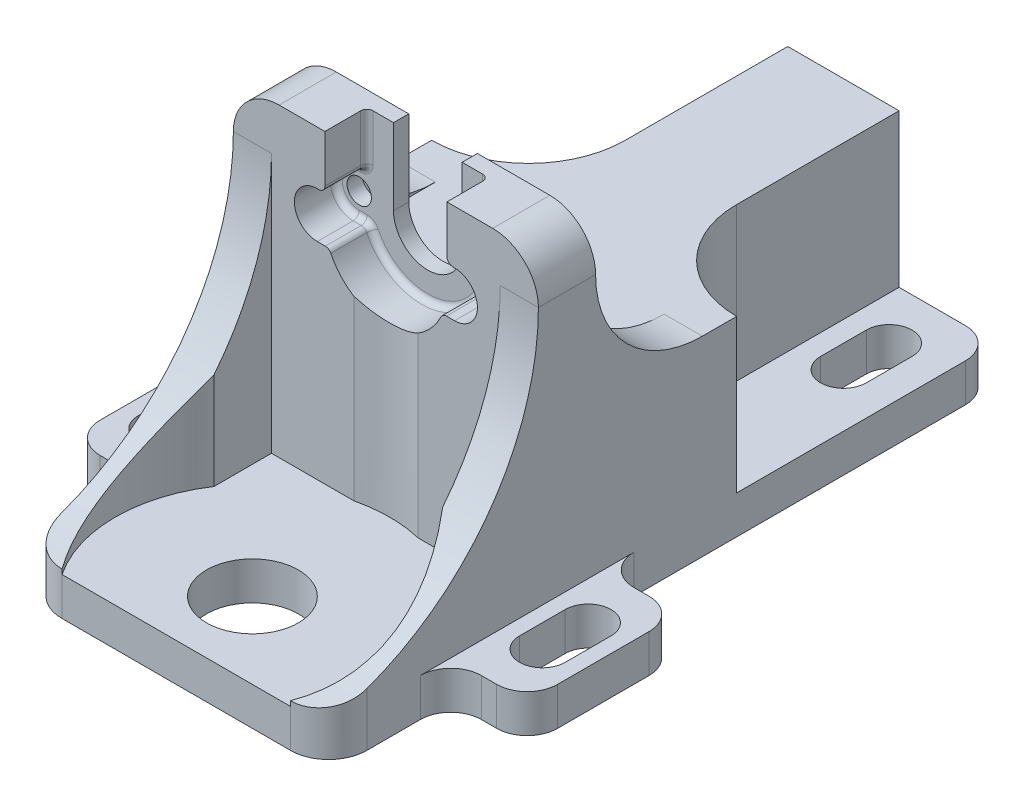
SolidWorks part; units mm, degrees
ref_plane "Front Plane" through (0, 0, 0) normal (0, 0, 1) x (1, 0, 0)
ref_plane "Top Plane" through (0, 0, 0) normal (0, 1, 0) x (1, 0, 0)
ref_plane "Right Plane" through (0, 0, 0) normal (1, 0, 0) x (0, 0, -1)
sketch "Sketch1" plane through (0, 0, 0) normal (0, 1, 0) x (1, 0, 0)
  line L1 (10, -25) -> (-10, -25)
  line L2 (10, -25) -> (10, 25)
  line L3 (10, 25) -> (-10, 25)
  line L4 (-10, -25) -> (-10, 25)
  line L5 (10, -25) -> (-10, 25) construction
  line L6 (10, 25) -> (-10, -25) construction
  point P0 (0, 0)
  dimension "D1" = 50
  dimension "D2" = 20
extrude "Boss-Extrude1" add sketch "Sketch1" along normal blind 12.525
sketch "Sketch2" plane through (0, 12.525, 0) normal (0, 1, 0) x (1, 0, 0)
  line L0 (-10, 25) -> (-10, -25) construction
  line L1 (-10, -1.25) -> (10, -1.25)
  line L2 (-10, -1.25) -> (-10, -5)
  line L3 (-10, -5) -> (10, -5)
  line L4 (10, -1.25) -> (10, -5)
  line L5 (10, -25) -> (10, 25) construction
  line L6 (-10, -25) -> (10, -25) construction
  dimension "D1" = 3.75
  dimension "D2" = 20
extrude "Boss-Extrude2" add sketch "Sketch2" along normal blind 10
sketch "Sketch3" plane through (0, 0, 5) normal (0, 0, 1) x (1, 0, 0)
  line L0 (-10, 22.525) -> (-10, 12.525) construction
  line L1 (-10, 12.525) -> (10, 12.525) construction
  line L2 (-10, 12.525) -> (-10, 22.525) construction
  line L3 (-10, 22.525) -> (10, 22.525) construction
  line L4 (10, 12.525) -> (10, 22.525) construction
  line L5 (-10, 12.525) -> (10, 22.525) construction
  line L6 (-10, 22.525) -> (10, 12.525) construction
  line L7 (-10, 12.525) -> (10, 12.525) construction
  line L8 (-4, 19.025) -> (-4, 22.525)
  line L9 (-4, 22.525) -> (4, 22.525)
  line L10 (4, 22.525) -> (4, 19.025)
  line L11 (0, 22.525) -> (0, 12.525) construction
  line L12 (-4.5, 17.525) -> (4.5, 17.525) construction
  line L13 (-4.5, 19.025) -> (-4, 19.025)
  line L14 (-4.5, 16.025) -> (-3.7081, 16.025)
  line L15 (4, 19.025) -> (4.5, 19.025)
  line L16 (3.7081, 16.025) -> (4.5, 16.025)
  line L17 (-4.5, 19.025) -> (-4.5, 16.025) construction
  arc A0 (-3.7081, 16.025) -> (3.7081, 16.025) centre (0, 17.525) ccw
  arc A3 (-4.5, 19.025) -> (-4.5, 16.025) centre (-4.5, 17.525) ccw
  arc A4 (4.5, 16.025) -> (4.5, 19.025) centre (4.5, 17.525) ccw
  point P20 (0, 11.35)
  dimension "D1" = 8
  dimension "D2" = 9
  dimension "D4" = 1.5
extrude "Cut-Extrude1" cut sketch "Sketch3" against normal offset from surface (2.75 mm away) 1 up to face at (2.5, 20.025, 1.25)
sketch "Sketch5" plane through (0, 0, 2.25) normal (0, 0, 1) x (1, 0, 0)
  line L0 (-2.25, 17.525) -> (-2.25, 22.525)
  line L1 (-4, 22.525) -> (4, 22.525) construction
  line L2 (-2.25, 22.525) -> (2.25, 22.525)
  line L3 (2.25, 22.525) -> (2.25, 17.525)
  arc A0 (-2.25, 17.525) -> (2.25, 17.525) centre (0, 17.525) ccw
  circle A1 centre (-4.5, 17.525) radius 0.8
  circle A2 centre (4.5, 17.525) radius 0.8
  dimension "D1" = 1.6
  dimension "D2" = 4.5
extrude "Cut-Extrude2" cut sketch "Sketch5" against normal through all
fillet "Fillet1" radius 0.4 13 edges at (4.104, 16.025, 2.25) (-4.104, 16.025, 2.25) (-4.25, 19.025, 2.25) (-4, 19.025, 3.625) (3.7081, 16.025, 3.625) (-3.7081, 16.025, 3.625) (6, 17.525, 2.25) (0, 13.525, 2.25) (-4, 20.775, 2.25) (-6, 17.525, 2.25) (4.25, 19.025, 2.25) (4, 19.025, 3.625) (4, 20.775, 2.25)
fillet "Fillet2" radius 3 2 edges at (10, 22.525, 3.125) (-10, 22.525, 3.125)
sketch "Sketch6" plane through (0, 12.525, 0) normal (0, 1, 0) x (1, 0, 0)
  line L2 (-10, -5) -> (10, -5)
  line L3 (-10, -5) -> (-10, -25)
  line L4 (-10, -25) -> (10, -25)
  line L5 (10, -5) -> (10, -25)
extrude "Cut-Extrude3" cut sketch "Sketch6" against normal offset from surface (10.025 mm away) 2.5 up to face at (0, 0, 0)
sketch "Sketch7" plane through (0, 2.5, 0) normal (0, 1, 0) x (1, 0, 0)
  line L1 (-2.25, -2.25) -> (2.25, -2.25) construction
  circle A0 centre (0, -13.75) radius 3.01
  dimension "D1" = 6.02
  dimension "D2" = 11.5
extrude "Cut-Extrude4" cut sketch "Sketch7" against normal through all
sketch "Sketch8" plane through (-10, 0, 0) normal (-1, 0, 0) x (0, 0, 1)
  line L0 (5, 19.525) -> (1.25, 19.525) construction
  line L1 (5, 2.5) -> (22.025, 2.5)
  line L2 (5, 2.5) -> (5, 19.525)
  line L4 (1.25, 12.525) -> (-5.75, 12.525)
  line L5 (1.25, 12.525) -> (1.25, 19.525)
  arc A0 (5, 19.525) -> (22.025, 2.5) centre (22.025, 19.525) ccw
  arc A1 (-5.75, 12.525) -> (1.25, 19.525) centre (-5.75, 19.525) ccw
extrude "Boss-Extrude3" add sketch "Sketch8" against normal blind 2.5
sketch "Sketch11" plane through (0, 12.525, 0) normal (0, 1, 0) x (1, 0, 0)
  line L0 (10, 25) -> (-10, 25) construction
  line L1 (-3.65, 25) -> (-10, 25)
  line L2 (-3.65, 25) -> (-3.65, 14.35)
  line L3 (-10, 25) -> (-10, 5.75) construction
  line L4 (-10, 25) -> (-10, 8)
  arc A0 (-10, 8) -> (-3.65, 14.35) centre (-10, 14.35) ccw
  dimension "D1" = 17
  dimension "D2" = 6.35
extrude "Cut-Extrude6" cut sketch "Sketch11" against normal up to surface (10.025 mm away) up to face at (-2.5, 2.5, 17.3417)
mirror "Mirror1" about plane through (0, 0, 0) normal (1, 0, 0) of "Cut-Extrude6", "Boss-Extrude3"
sketch "Sketch13" plane through (0, 0, 0) normal (0, -1, 0) x (1, 0, 0)
  line L0 (10, 25) -> (10, -25) construction
  line L1 (-10, 25) -> (10, 25)
  line L2 (-10, 25) -> (-10, 18.75)
  line L3 (-10, 18.75) -> (10, 18.75)
  line L4 (10, 25) -> (10, 18.75)
  circle A0 centre (0, 13.75) radius 3.01 construction
  dimension "D1" = 5
extrude "Cut-Extrude8" cut sketch "Sketch13" against normal through all
sketch "Sketch14" plane through (0, 0, 0) normal (0, -1, 0) x (1, 0, 0)
  line L0 (0, 23.25) -> (0, -25) construction
  line L1 (15, 0.74) -> (-15, 0.74)
  line L2 (15, 0.74) -> (15, 10.74)
  line L3 (15, 10.74) -> (-15, 10.74)
  line L4 (-15, 0.74) -> (-15, 10.74)
  line L5 (10, -25) -> (-10, -25) construction
  line L6 (-10, -25) -> (-10, 18.75) construction
  circle A1 centre (0, 13.75) radius 3.01 construction
  dimension "D1" = 10
  dimension "D2" = 5
extrude "Boss-Extrude4" add sketch "Sketch14" against normal up to surface (2.5 mm away) up to face at (0, 2.5, 11.875)
sketch "Sketch12" plane through (0, 2.5, 0) normal (0, 1, 0) x (1, 0, 0)
  line L0 (-6.5, 21.5) -> (-6.5, 18.5) construction
  line L1 (-5, 21.5) -> (-5, 18.5)
  line L2 (-8, 21.5) -> (-8, 18.5)
  line L3 (6.5, 21.5) -> (6.5, 18.5) construction
  line L4 (8, 21.5) -> (8, 18.5)
  line L5 (5, 21.5) -> (5, 18.5)
  line L6 (-12.5, -7.24) -> (-12.5, -4.24) construction
  line L7 (-14, -7.24) -> (-14, -4.24)
  line L8 (-11, -7.24) -> (-11, -4.24)
  line L9 (0, 25) -> (0, -25) construction
  line L10 (3.65, 25) -> (-3.65, 25) construction
  line L12 (-10, 8) -> (-10, 25) construction
  line L13 (-10, 25) -> (-3.65, 25) construction
  line L14 (12.5, -7.24) -> (12.5, -4.24) construction
  line L15 (11, -7.24) -> (11, -4.24)
  line L16 (14, -7.24) -> (14, -4.24)
  line L17 (15, -10.74) -> (10, -10.74) construction
  line L18 (10, -10.74) -> (15, -10.74) construction
  line L19 (10, -10.74) -> (10, -0.74) construction
  line L20 (10, -0.74) -> (15, -0.74) construction
  line L21 (15, -10.74) -> (15, -0.74) construction
  line L22 (10, -10.74) -> (15, -0.74) construction
  line L23 (10, -0.74) -> (15, -10.74) construction
  line L24 (10, -10.74) -> (10, -0.74) construction
  arc A0 (-5, 21.5) -> (-8, 21.5) centre (-6.5, 21.5) ccw
  arc A1 (-8, 18.5) -> (-5, 18.5) centre (-6.5, 18.5) ccw
  arc A2 (8, 21.5) -> (5, 21.5) centre (6.5, 21.5) ccw
  arc A3 (5, 18.5) -> (8, 18.5) centre (6.5, 18.5) ccw
  arc A4 (-14, -7.24) -> (-11, -7.24) centre (-12.5, -7.24) ccw
  arc A5 (-11, -4.24) -> (-14, -4.24) centre (-12.5, -4.24) ccw
  arc A6 (11, -7.24) -> (14, -7.24) centre (12.5, -7.24) ccw
  arc A7 (14, -4.24) -> (11, -4.24) centre (12.5, -4.24) ccw
  point P2 (-6.5, 20)
  point P7 (6.5, 20)
  point P16 (-12.5, -5.74)
  point P26 (12.5, -5.74)
  point P37 (12.5, -5.74)
  dimension "D1" = 1.5
  dimension "D5" = 3.5
  dimension "D2" = 3
  dimension "D4" = 2
extrude "Cut-Extrude7" cut sketch "Sketch12" against normal through all
fillet "Fillet3" radius 2 10 edges at (10, 1.25, -25) (-10, 1.25, -25) (-10, 1.25, 0.74) (-10, 1.25, 10.74) (10, 1.25, 10.74) (10, 1.25, 0.74) (15, 1.25, 0.74) (-15, 1.25, 0.74) (-15, 1.25, 10.74) (15, 1.25, 10.74)
fillet "Fillet4" radius 2.5 2 edges at (10, 1.409, 18.75) (-10, 1.409, 18.75)
sketch "Sketch15" plane through (0, 2.5, 0) normal (0, 1, 0) x (1, 0, 0)
  circle A0 centre (0, -13.75) radius 9
  dimension "D1" = 18
extrude "Cut-Extrude10" cut sketch "Sketch15" along normal through all contours A0
